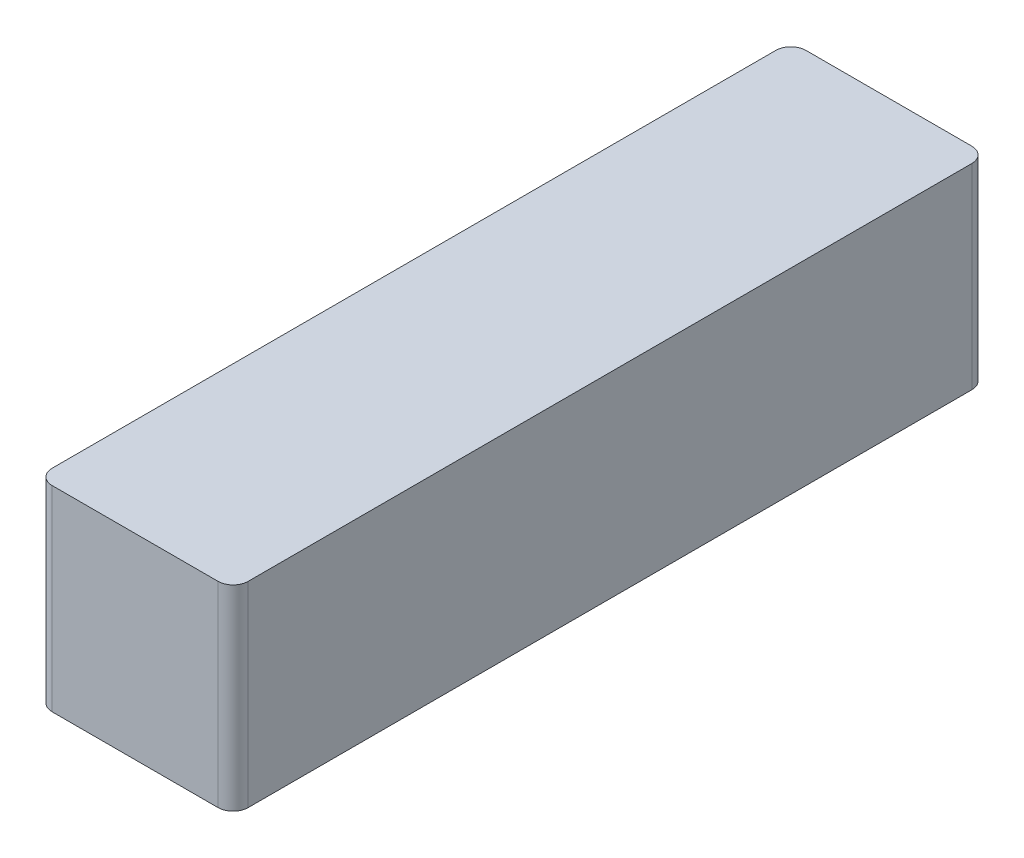
SolidWorks part; units mm, degrees
ref_plane "Front" through (0, 0, 0) normal (0, 0, 1) x (1, 0, 0)
ref_plane "Top" through (0, 0, 0) normal (0, 1, 0) x (1, 0, 0)
ref_plane "Right" through (0, 0, 0) normal (1, 0, 0) x (0, 0, -1)
sketch "Sketch1" plane through (0, 0, 0) normal (0, 0, 1) x (1, 0, 0)
  line L1 (-1.651, 1.651) -> (1.651, 1.651)
  line L2 (-1.651, 1.651) -> (-1.651, -1.651)
  line L3 (-1.651, -1.651) -> (1.651, -1.651)
  line L4 (1.651, 1.651) -> (1.651, -1.651)
  line L5 (-1.651, 1.651) -> (1.651, -1.651) construction
  line L6 (-1.651, -1.651) -> (1.651, 1.651) construction
  point P0 (0, 0)
  dimension "D1" = 3.302
extrude "Boss-Extrude1" add sketch "Sketch1" along normal blind 12.7
fillet "Fillet1" radius 0.254 4 edges at (-1.651, 0, 0) (1.651, 0, 0) (-1.651, 0, 12.7) (1.651, 0, 12.7)
